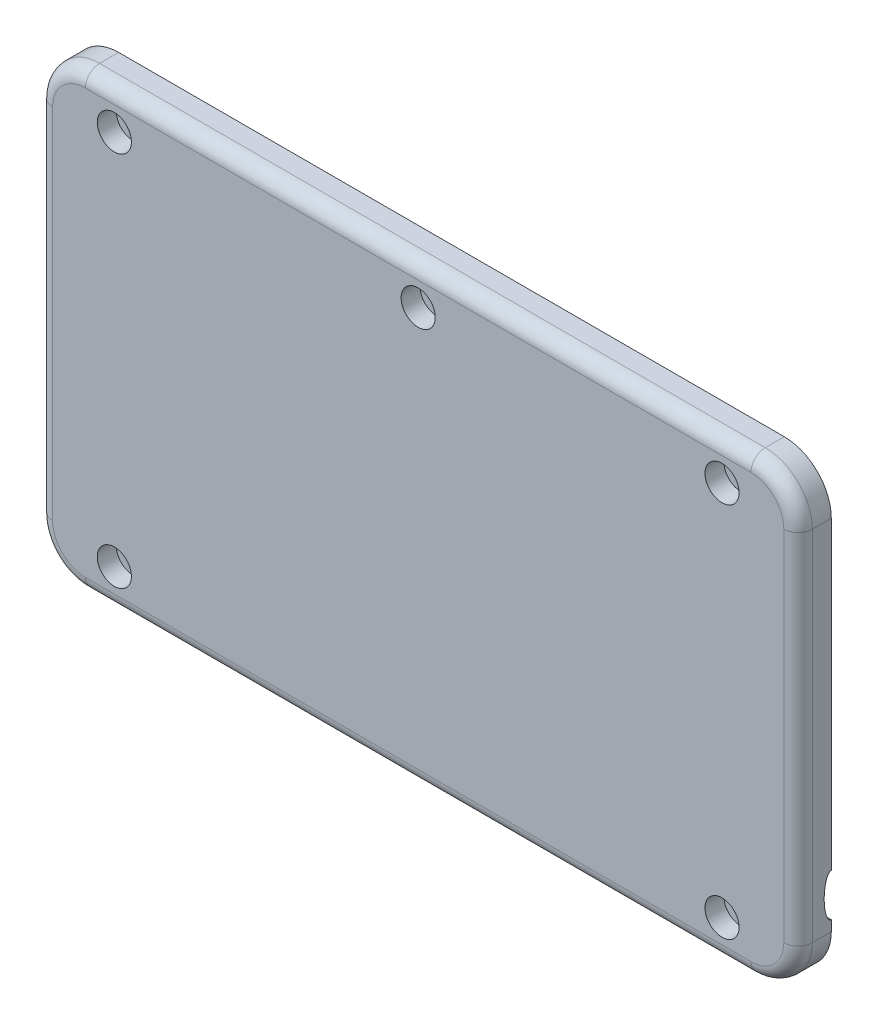
SolidWorks part; units mm, degrees
ref_plane "Front Plane" through (0, 0, 0) normal (0, 0, 1) x (1, 0, 0)
ref_plane "Top Plane" through (0, 0, 0) normal (0, 1, 0) x (1, 0, 0)
ref_plane "Right Plane" through (0, 0, 0) normal (1, 0, 0) x (0, 0, -1)
sketch "Sketch1" plane through (0, 0, 0) normal (0, 0, 1) x (1, 0, 0)
  line L3 (-185.46, 115.84) -> (-7.5, 115.84) construction
  line L4 (5.08, 103.26) -> (5.08, 21.725) construction
  line L6 (5.08, 103.26) -> (5.08, 21.725)
  line L7 (-185.46, 115.84) -> (-7.5, 115.84)
  line L8 (-198.04, 7.5) -> (-198.04, 103.26)
  line L11 (5.08, 7.5) -> (5.08, 21.725)
  line L12 (-7.5, -5.08) -> (-185.46, -5.08) construction
  line L13 (-7.5, -5.08) -> (-185.46, -5.08)
  arc A0 (-198.04, 7.5) -> (-185.46, -5.08) centre (-185.46, 7.5) ccw construction
  arc A1 (-185.46, 115.84) -> (-198.04, 103.26) centre (-185.46, 103.26) ccw construction
  arc A2 (5.08, 103.26) -> (-7.5, 115.84) centre (-7.5, 103.26) ccw construction
  arc A3 (-7.5, -5.08) -> (5.08, 7.5) centre (-7.5, 7.5) ccw construction
  arc A4 (-7.5, -5.08) -> (5.08, 7.5) centre (-7.5, 7.5) ccw
  arc A5 (5.08, 103.26) -> (-7.5, 115.84) centre (-7.5, 103.26) ccw
  arc A6 (-185.46, 115.84) -> (-198.04, 103.26) centre (-185.46, 103.26) ccw
  arc A7 (-198.04, 7.5) -> (-185.46, -5.08) centre (-185.46, 7.5) ccw
  point P2 (-34.5462, -5.08)
  point P9 (0, 0)
extrude "Boss-Extrude1" add sketch "Sketch1" along normal up to surface (8.89 mm away)
fillet "Fillet1" radius 3.81 8 edges at (-194.3554, -1.3954, 8.89) (-198.04, 55.38, 8.89) (-194.3554, 112.1554, 8.89) (-96.48, 115.84, 8.89) (1.3954, 112.1554, 8.89) (5.08, 55.38, 8.89) (1.3954, -1.3954, 8.89) (-96.48, -5.08, 8.89)
shell "Shell1" thickness 2.54
sketch "Sketch7" plane through (0, 0, 0) normal (0, 0, -1) x (-1, 0, 0)
  line L0 (-2.54, 7.5) -> (-2.54, 103.26) construction
  line L1 (-2.54, 7.5) -> (-2.54, 103.26)
  line L2 (2.54, 111.9893) -> (2.54, 95.52) construction
  line L3 (2.54, 10.295) -> (2.54, -1.2293) construction
  line L4 (2.54, 92.98) -> (2.54, 21.725) construction
  line L5 (2.54, 111.9893) -> (2.54, 95.52)
  line L6 (2.54, 10.295) -> (2.54, -1.2293)
  line L7 (2.54, 92.98) -> (2.54, 21.725)
  line L8 (2.54, 95.52) -> (2.54, 92.98)
  line L9 (2.54, 21.725) -> (2.54, 10.295)
  arc A0 (-2.54, 7.5) -> (7.5, -2.54) centre (7.5, 7.5) ccw construction
  arc A1 (7.5, 113.3) -> (-2.54, 103.26) centre (7.5, 103.26) ccw construction
  arc A2 (-2.54, 7.5) -> (2.54, -1.2293) centre (7.5, 7.5) ccw
  arc A3 (2.54, 111.9893) -> (-2.54, 103.26) centre (7.5, 103.26) ccw
extrude "Boss-Extrude4" add sketch "Sketch7" against normal up to next
ref_plane "Plane1" through (0, 0, 0.127) normal (0, 0, -1) x (-1, 0, 0)
sketch "Sketch2" plane through (0, 0, 0.127) normal (0, 0, -1) x (-1, 0, 0)
  line L0 (13.97, 110.5987) -> (13.97, 113.3) construction
  line L1 (16.51, 113.3) -> (16.51, 110.5987) construction
  line L2 (13.97, 110.5987) -> (13.97, 113.3)
  line L3 (16.51, 113.3) -> (16.51, 110.5987)
  line L4 (95.21, 110.5987) -> (95.21, 113.3) construction
  line L5 (97.75, 113.3) -> (97.75, 110.5987) construction
  line L6 (95.21, 110.5987) -> (95.21, 113.3)
  line L7 (97.75, 113.3) -> (97.75, 110.5987)
  line L8 (176.45, 110.5987) -> (176.45, 113.3) construction
  line L9 (178.99, 113.3) -> (178.99, 110.5987) construction
  line L10 (176.45, 110.5987) -> (176.45, 113.3)
  line L11 (178.99, 113.3) -> (178.99, 110.5987)
  line L12 (176.45, -2.54) -> (176.45, 0.1613) construction
  line L13 (178.99, 0.1613) -> (178.99, -2.54) construction
  line L14 (176.45, -2.54) -> (176.45, 0.1613)
  line L15 (178.99, 0.1613) -> (178.99, -2.54)
  line L16 (13.97, -2.54) -> (13.97, 0.1613) construction
  line L17 (16.51, 0.1613) -> (16.51, -2.54) construction
  line L18 (13.97, -2.54) -> (13.97, 0.1613)
  line L19 (16.51, 0.1613) -> (16.51, -2.54)
  line L20 (13.97, -2.54) -> (16.51, -2.54)
  line L21 (176.45, -2.54) -> (178.99, -2.54)
  line L22 (176.45, 113.3) -> (178.99, 113.3)
  line L23 (95.21, 113.3) -> (97.75, 113.3)
  line L24 (13.97, 113.3) -> (16.51, 113.3)
  arc A0 (13.97, 110.5987) -> (16.51, 110.5987) centre (15.24, 105.68) ccw construction
  arc A1 (13.97, 110.5987) -> (16.51, 110.5987) centre (15.24, 105.68) ccw
  arc A2 (95.21, 110.5987) -> (97.75, 110.5987) centre (96.48, 105.68) ccw construction
  arc A3 (95.21, 110.5987) -> (97.75, 110.5987) centre (96.48, 105.68) ccw
  arc A4 (176.45, 110.5987) -> (178.99, 110.5987) centre (177.72, 105.68) ccw construction
  arc A5 (176.45, 110.5987) -> (178.99, 110.5987) centre (177.72, 105.68) ccw
  arc A6 (178.99, 0.1613) -> (176.45, 0.1613) centre (177.72, 5.08) ccw construction
  arc A7 (178.99, 0.1613) -> (176.45, 0.1613) centre (177.72, 5.08) ccw
  arc A8 (16.51, 0.1613) -> (13.97, 0.1613) centre (15.24, 5.08) ccw construction
  arc A9 (16.51, 0.1613) -> (13.97, 0.1613) centre (15.24, 5.08) ccw
extrude "Boss-Extrude2" add sketch "Sketch2" against normal up to next
sketch "Sketch3" plane through (0, 0, 0.127) normal (0, 0, -1) x (-1, 0, 0)
  circle A0 centre (15.24, 105.68) radius 3.5052
  circle A1 centre (96.48, 105.68) radius 3.5052
  circle A2 centre (177.72, 105.68) radius 3.5052
  circle A3 centre (177.72, 5.08) radius 3.5052
  circle A4 centre (15.24, 5.08) radius 3.5052
  dimension "D1" = 7.0104
extrude "Boss-Extrude3" add sketch "Sketch3" along normal blind 1.5875
hole_wizard "CBORE for #8 Pan Head Machine Screw1" positions "3DSketch1" profile "Sketch4" counterbore size "#8" standard "ANSI Inch" end condition through all
sketch3d "3DSketch1"
  circle A0 centre (-15.24, 5.08, -1.4605) radius 3.5052 construction
  circle A1 centre (-177.72, 5.08, -1.4605) radius 3.5052 construction
  circle A2 centre (-177.72, 105.68, -1.4605) radius 3.5052 construction
  circle A3 centre (-96.48, 105.68, -1.4605) radius 3.5052 construction
  circle A4 centre (-15.24, 105.68, -1.4605) radius 3.5052 construction
  point P39 (-15.24, 5.08, 8.89)
  point P40 (-177.72, 5.08, 8.89)
  point P41 (-177.72, 105.68, 8.89)
  point P46 (-15.24, 5.08, -4.9657)
  point P50 (-177.72, 5.08, -4.9657)
  point P54 (-177.72, 105.68, -4.9657)
  point P55 (-96.48, 105.68, 8.89)
  point P57 (-15.24, 105.68, 8.89)
  point P63 (-96.48, 105.68, -4.9657)
  point P67 (-15.24, 105.68, -4.9657)
sketch "Sketch4" plane through (-15.24, 5.08, 8.89) normal (1, 0, 0) x (0, -1, 0)
  line L0 (0, 0) -> (0, 10.3505)
  line L1 (0, 10.3505) -> (2.4574, 10.3505)
  line L3 (2.4574, 10.3505) -> (2.4574, 5.08)
  line L4 (2.4574, 5.08) -> (4.5644, 5.08)
  line L5 (4.5644, 5.08) -> (4.5644, 0)
  line L7 (4.5644, 0) -> (0, 0)
  line L11 (0, -6.35) -> (0, 107.95) construction
  dimension "Thru Hole Dia." = 4.9149
  dimension "Thru Hole Depth" = 10.3505
  dimension "C'Bore Dia." = 9.1288
  dimension "C'Bore Depth" = 5.08
sketch "Sketch5" plane through (-198.04, 192.96, 0) normal (1, 0, 0) x (0, 1, 0)
  line L0 (-176.95, -3.81) -> (-176.95, 3.7609) construction
  line L4 (-171.235, 0) -> (-182.665, 0)
  line L5 (-182.665, -3.81) -> (-182.665, 0) construction
  line L13 (-89.7, 0) -> (-185.46, 0) construction
  circle A0 centre (-176.95, -3.81) radius 5.715 construction
  arc A2 (-182.665, -3.81) -> (-171.235, -3.81) centre (-176.95, -3.81) ccw construction
  ellipse E0 centre (-176.95, 0) end of major axis (-182.665, 0) minor radius 1.905 (-182.665, 0) -> (-171.235, 0) cw
  point P6 (-34.17, 0)
  point P7 (0, 0)
  point P19 (0, 0)
  point P21 (0, 0)
  point P22 (-171.235, 0.1696)
extrude "Cut-Extrude1" cut sketch "Sketch5" along normal up to next
sketch "Sketch6" plane through (5.08, -160.94, 0) normal (-1, 0, 0) x (0, -1, 0)
  line L0 (-176.95, -3.81) -> (-176.95, 3.7609) construction
  line L1 (-168.44, 0) -> (-264.2, 0) construction
  line L2 (-171.235, 0) -> (-171.235, -3.81) construction
  line L4 (-171.235, 0) -> (-182.665, 0)
  circle A0 centre (-176.95, -3.81) radius 5.715 construction
  ellipse E0 centre (-176.95, 0) end of major axis (-182.665, 0) minor radius 1.905 (-182.665, 0) -> (-171.235, 0) cw
  point P6 (-34.17, 0)
  point P7 (0, 0)
  point P19 (0, 0)
  point P21 (0, 0)
  point P22 (-171.235, 0.1696)
extrude "Cut-Extrude3" cut sketch "Sketch6" along normal up to next
sketch "Sketch8" plane through (-198.04, -139.35, 0) normal (-1, 0, 0) x (0, -1, 0)
  line L0 (-176.95, -3.81) -> (-176.95, 3.7609) construction
  line L1 (-121.69, 0) -> (56.27, 0) construction
  line L2 (-171.235, -3.81) -> (-171.235, 0) construction
  line L4 (-171.235, 0) -> (-182.665, 0)
  circle A0 centre (-176.95, -3.81) radius 5.715 construction
  ellipse E0 centre (-176.95, 0) end of major axis (-182.665, 0) minor radius 1.905 (-182.665, 0) -> (-171.235, 0) cw
  point P4 (-211.639, 0)
  point P6 (-34.17, 0)
  point P7 (0, 0)
  point P13 (0, 0)
  point P19 (0, 0)
  point P21 (0, 0)
  point P22 (-171.235, 0.1696)
extrude "Cut-Extrude4" cut sketch "Sketch8" against normal up to next
